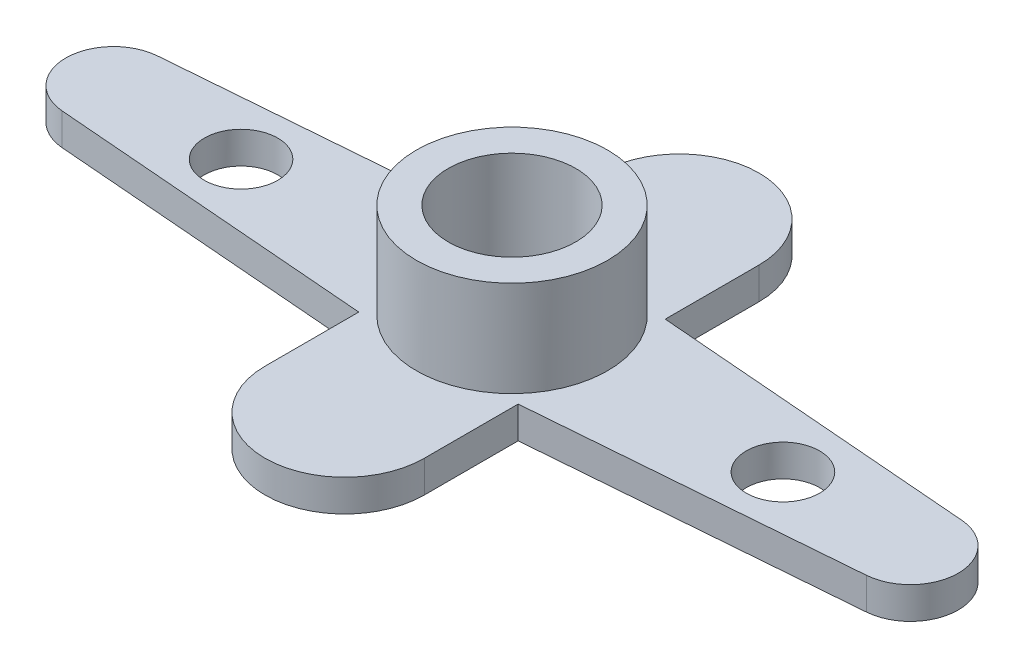
SolidWorks part; units mm, degrees
material "uhlíková ocel 7850"
ref_plane "Přední rovina" through (0, 0, 0) normal (0, 0, 1) x (1, 0, 0)
ref_plane "Horní rovina" through (0, 0, 0) normal (0, 1, 0) x (1, 0, 0)
ref_plane "Pravá rovina" through (0, 0, 0) normal (1, 0, 0) x (0, 0, -1)
sketch "Skica1" plane through (0, 0, 0) normal (0, 1, 0) x (1, 0, 0)
  line L0 (0, 0) -> (-12.5, 0) construction
  line L1 (-12.62, 1.4952) -> (-2.5, 2.3074)
  line L2 (0, 15.429) -> (0, 0) construction
  line L3 (-12.5, 0) -> (-39.2821, 0) construction
  line L4 (12.62, 1.4952) -> (2.5, 2.3074)
  line L5 (12.62, -1.4952) -> (2.5, -2.3074)
  line L6 (-12.62, -1.4952) -> (-2.5, -2.3074)
  line L7 (0, 2.5) -> (-5.8693, 2.5) construction
  line L8 (-2.5, 2.3074) -> (-2.5, 5.25)
  line L9 (2.5, 2.3074) -> (2.5, 5.25)
  line L10 (2.5, -2.3074) -> (2.5, -5.25)
  line L11 (-2.5, -2.3074) -> (-2.5, -5.25)
  circle A0 centre (0, 0) radius 2
  arc A1 (2.5, -5.25) -> (-2.5, -5.25) centre (0, -5.25) cw
  arc A2 (-12.62, 1.4952) -> (-12.62, -1.4952) centre (-12.5, 0) ccw
  arc A3 (12.62, 1.4952) -> (12.62, -1.4952) centre (12.5, 0) cw
  arc A5 (2.5, 5.25) -> (-2.5, 5.25) centre (0, 5.25) ccw
  point P19 (0, 7.75)
  dimension "D1" = 4
  dimension "D2" = 1.5
  dimension "D3" = 2.5
  dimension "D5" = 15.5
  dimension "D7" = 2.5
  dimension "D4" = 12.5
  dimension "D6" = 5
extrude "Přidat vysunutím1" add sketch "Skica1" along normal blind 1
sketch "Skica2" plane through (0, 1, 0) normal (0, 1, 0) x (1, 0, 0)
  line L0 (-8.5, 0) -> (0, 0) construction
  line L1 (0, 0) -> (0, -4.2214) construction
  line L2 (0, 0) -> (8.5, 0) construction
  circle A0 centre (-8.5, 0) radius 1.15
  circle A1 centre (8.5, 0) radius 1.15
  dimension "D1" = 2.3
  dimension "D2" = 17
extrude "Odebrat vysunutím1" cut sketch "Skica2" against normal blind 2
sketch "Skica3" plane through (0, 1, 0) normal (0, 1, 0) x (1, 0, 0)
  circle A1 centre (0, 0) radius 3
  circle A2 centre (0, 0) radius 2
  circle A3 centre (0, 0) radius 2 construction
  dimension "D1" = 6
extrude "Přidat vysunutím2" add sketch "Skica3" along normal blind 3
